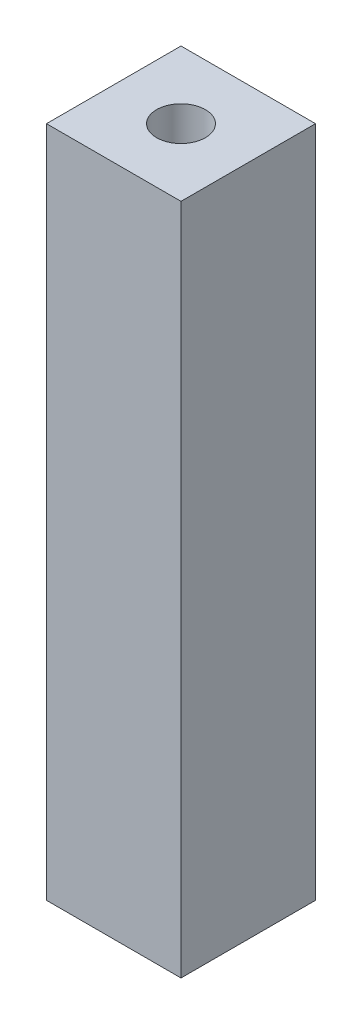
SolidWorks part; units mm, degrees
ref_plane "Front Plane" through (0, 0, 0) normal (0, 0, 1) x (1, 0, 0)
ref_plane "Top Plane" through (0, 0, 0) normal (0, 1, 0) x (1, 0, 0)
ref_plane "Right Plane" through (0, 0, 0) normal (1, 0, 0) x (0, 0, -1)
sketch "Sketch1" plane through (0, 0, 0) normal (0, 1, 0) x (1, 0, 0)
  line L1 (-4, -4) -> (4, -4)
  line L2 (-4, -4) -> (-4, 4)
  line L3 (-4, 4) -> (4, 4)
  line L4 (4, -4) -> (4, 4)
  line L5 (-4, -4) -> (4, 4) construction
  line L6 (-4, 4) -> (4, -4) construction
  point P0 (0, 0)
  dimension "D1" = 8
extrude "Boss-Extrude1" add sketch "Sketch1" along normal blind 40
sketch "Sketch2" plane through (0, 40, 0) normal (0, 1, 0) x (1, 0, 0)
  circle A0 centre (0, 0) radius 1.45
  dimension "D1" = 2.9
extrude "Cut-Extrude1" cut sketch "Sketch2" against normal through all
